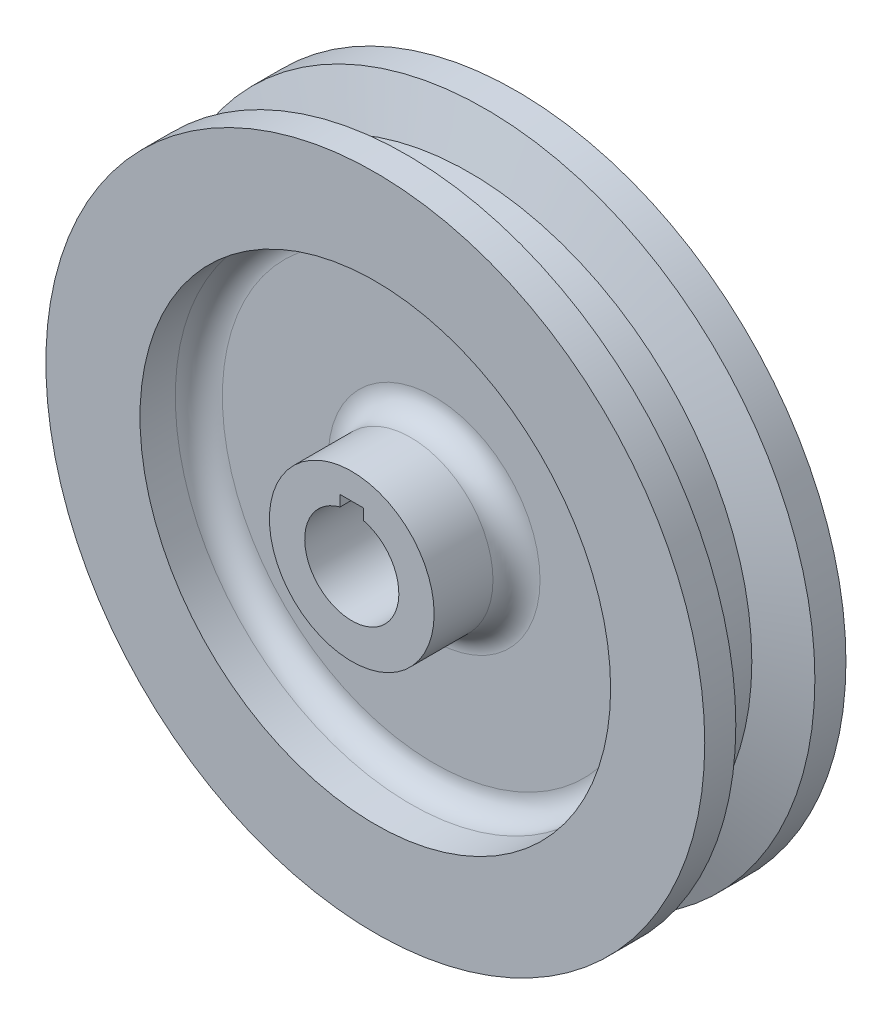
SolidWorks part; units mm, degrees
other "DetailItem1"
material "Cast Carbon Steel"
ref_plane "Frontal" through (0, 0, 0) normal (0, 0, 1) x (1, 0, 0)
ref_plane "Horizontal" through (0, 0, 0) normal (0, 1, 0) x (1, 0, 0)
ref_plane "Profile" through (0, 0, 0) normal (1, 0, 0) x (0, 0, -1)
sketch "Sketch1" plane through (0, 0, 0) normal (1, 0, 0) x (0, 0, -1)
  line L0 (-1, 0.5) -> (1, 0.5)
  line L1 (1, 0.5) -> (1, 0.875)
  line L2 (1, 0.875) -> (0.375, 0.875)
  line L3 (0.125, 1.125) -> (0.125, 2.25)
  line L4 (0.375, 2.5) -> (0.75, 2.5)
  line L5 (-1, 0.5) -> (-1, 0.875)
  line L6 (-1, 0.875) -> (-0.375, 0.875)
  line L7 (-0.125, 1.125) -> (-0.125, 2.25)
  line L8 (-0.375, 2.5) -> (-0.75, 2.5)
  line L9 (-0.75, 3.5) -> (-0.75, 2.5)
  line L10 (0.75, 2.5) -> (0.75, 3.5)
  line L11 (-0.25, 3) -> (0.25, 3)
  line L12 (-0.75, 3.5) -> (-0.42, 3.5)
  line L13 (-0.42, 3.5) -> (-0.25, 3)
  line L14 (0.25, 3) -> (0.42, 3.5)
  line L15 (0.42, 3.5) -> (0.75, 3.5)
  line L16 (-1.4799, 0) -> (1.1859, 0)
  arc A0 (-0.375, 2.5) -> (-0.125, 2.25) centre (-0.375, 2.25) cw
  arc A1 (0.375, 2.5) -> (0.125, 2.25) centre (0.375, 2.25) ccw
  arc A2 (-0.125, 1.125) -> (-0.375, 0.875) centre (-0.375, 1.125) cw
  arc A3 (0.375, 0.875) -> (0.125, 1.125) centre (0.375, 1.125) cw
  point P0 (-1, 0.5)
  point P1 (-1, 0.875)
  point P2 (-0.125, 0.875)
  point P3 (1, 0.5)
  point P4 (1, 0.875)
  point P6 (0.125, 0.875)
  point P7 (-0.125, 2.5)
  point P8 (0.125, 2.5)
  point P9 (0.75, 2.5)
  point P10 (-0.75, 2.5)
  point P23 (-0.125, 2.5)
  point P26 (0.125, 2.5)
  point P29 (-0.125, 0.875)
  point P32 (0.125, 0.875)
  point P33 (-0.75, 3.5)
  point P34 (0.75, 3.5)
  point P36 (0.25, 3)
  point P38 (-0.25, 3)
  point P39 (-0.42, 3.5)
  point P40 (0.42, 3.5)
  dimension "D1" = 0.25
  dimension "D2" = 0.25
  dimension "D3" = 0.25
  dimension "D4" = 0.25
revolve "Revolve1" add sketch "Sketch1" angle 360 about L16
sketch "Sketch2" plane through (0, 0, 1) normal (0, 0, 1) x (1, 0, 0)
  line L0 (-0.125, 0.6) -> (0.125, 0.6)
  line L1 (0.125, 0.6) -> (0.125, 0.2292)
  line L2 (0.125, 0.2292) -> (-0.125, 0.2292)
  line L3 (-0.125, 0.2292) -> (-0.125, 0.6)
  point P0 (0.125, 0.6)
  point P1 (-0.125, 0.6)
extrude "Cut-Extrude1" cut sketch "Sketch2" against normal blind 20.6248
